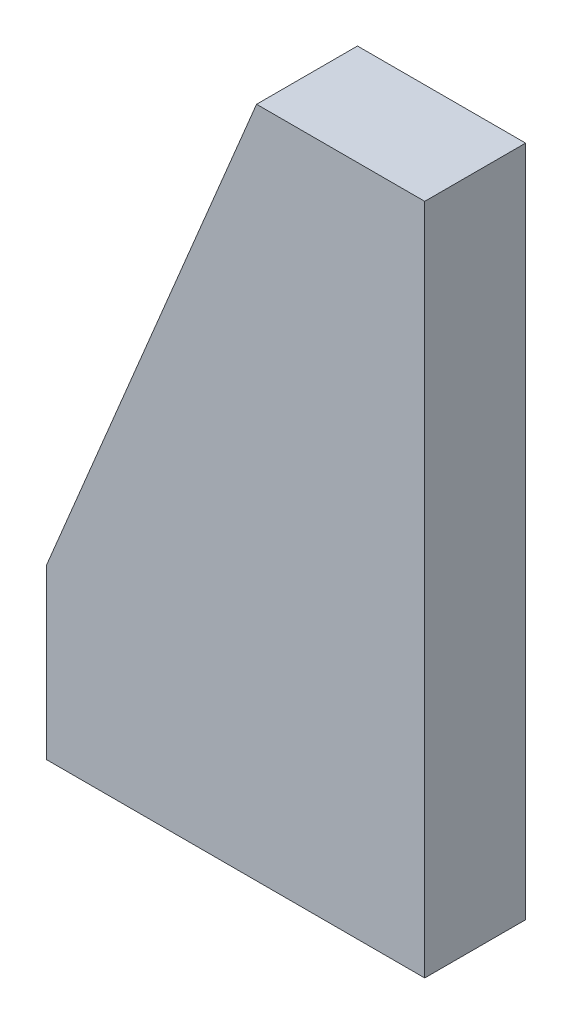
SolidWorks part; units mm, degrees
material "1023 Листовая углеродистая сталь (SS)"
ref_plane "Front" through (0, 0, 0) normal (0, 0, 1) x (1, 0, 0)
ref_plane "Top" through (0, 0, 0) normal (0, 1, 0) x (1, 0, 0)
ref_plane "Right" through (0, 0, 0) normal (1, 0, 0) x (0, 0, -1)
sketch "Sketch1" plane through (0, 0, 0) normal (0, 0, 1) x (1, 0, 0)
  line L0 (0, 0) -> (45, 0)
  line L1 (45, 0) -> (45, 80)
  line L2 (45, 80) -> (25, 80)
  line L3 (25, 80) -> (0, 20)
  line L4 (0, 20) -> (0, 0)
  dimension "D1" = 45
  dimension "D2" = 80
  dimension "D3" = 20
  dimension "D4" = 20
extrude "Extrude1" add sketch "Sketch1" along normal blind 12
